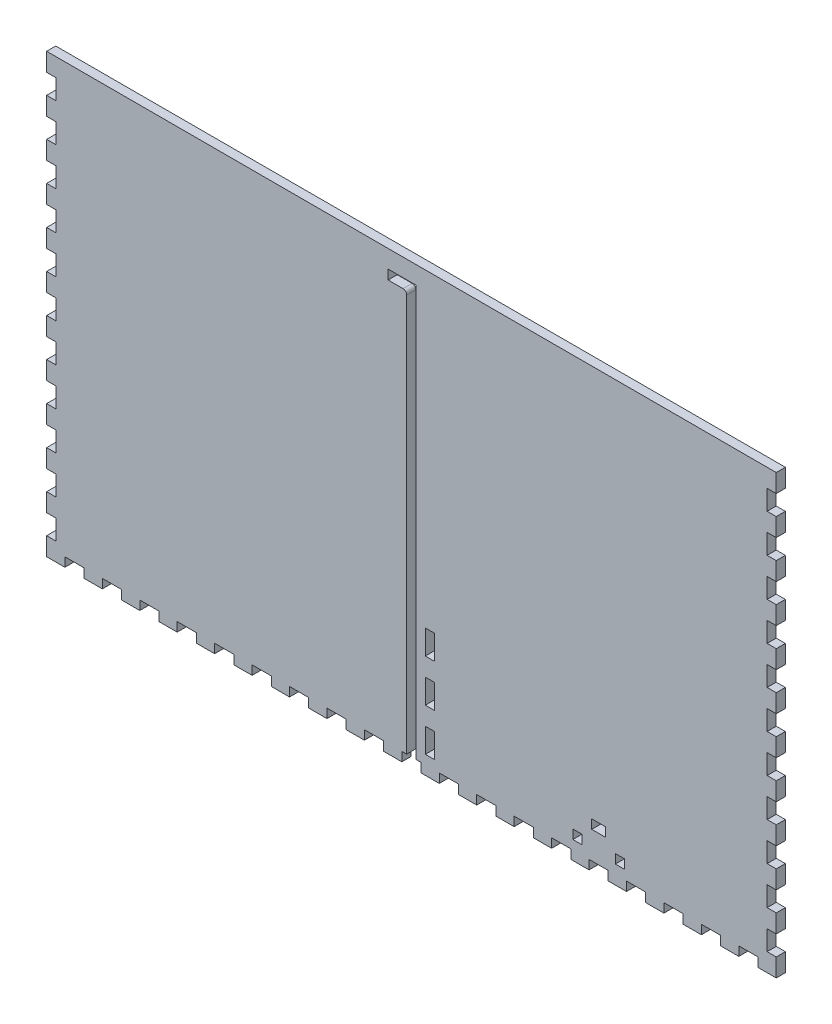
SolidWorks part; units mm, degrees
material "Acrylic (Medium-high impact)"
ref_plane "Front Plane" through (0, 0, 0) normal (0, 0, 1) x (1, 0, 0)
ref_plane "Top Plane" through (0, 0, 0) normal (0, 1, 0) x (1, 0, 0)
ref_plane "Right Plane" through (0, 0, 0) normal (1, 0, 0) x (0, 0, -1)
sketch "Sketch1" plane through (0, 0, 0) normal (0, 1, 0) x (1, 0, 0)
  line L1 (-254, 95.25) -> (254, 95.25)
  line L2 (-254, 95.25) -> (-254, -95.25)
  line L3 (-254, -95.25) -> (254, -95.25)
  line L4 (254, 95.25) -> (254, -95.25)
  point P4 (-254, 0)
  point P6 (0, 95.25)
  dimension "D1" = 190.5
  dimension "D2" = 508
extrude "Boss-Extrude1" add sketch "Sketch1" along normal blind 6.35
sketch "Sketch2" plane through (0, 6.35, 0) normal (0, 1, 0) x (1, 0, 0)
  line L0 (254, -95.25) -> (254, 95.25) construction
  line L1 (-254, 95.25) -> (254, 95.25)
  line L2 (-254, 95.25) -> (-254, -95.25)
  line L3 (-254, -95.25) -> (254, -95.25)
  line L4 (254, 95.25) -> (254, -95.25)
  line L5 (-254, -95.25) -> (254, -95.25) construction
  line L7 (-247.65, 88.9) -> (247.65, 88.9)
  line L8 (-247.65, 88.9) -> (-247.65, -88.9)
  line L9 (-247.65, -88.9) -> (247.65, -88.9)
  line L10 (247.65, 88.9) -> (247.65, -88.9)
  point P7 (-247.65, 0)
  point P14 (-254, 0)
  point P15 (0, -88.9)
  point P16 (0, -95.25)
  point P17 (247.65, 0)
  point P18 (254, 0)
  dimension "D1" = 6.35
  dimension "D2" = 6.35
extrude "Boss-Extrude2" add sketch "Sketch2" along normal blind 298.45
sketch "Sketch3" plane through (0, 0, 95.25) normal (0, 0, 1) x (1, 0, 0)
  line L0 (0, 304.8) -> (0, 0) construction
  line L1 (-254, 304.8) -> (254, 304.8) construction
  line L2 (-247.65, 6.35) -> (247.65, 6.35) construction
  line L4 (-3.302, 283.21) -> (-3.302, 6.35)
  line L5 (-3.302, 6.35) -> (3.302, 6.35)
  line L6 (3.302, 292.354) -> (3.302, 6.35)
  line L7 (3.302, 292.354) -> (-16.256, 292.354)
  line L9 (-5.842, 285.75) -> (-16.256, 285.75)
  line L10 (-16.256, 292.354) -> (-16.256, 285.75)
  line L11 (3.302, 101.6) -> (16.002, 101.6) construction
  line L12 (-254, 0) -> (254, 0) construction
  line L13 (12.827, 88.9) -> (12.827, 101.6) construction
  line L14 (9.652, 88.9) -> (16.002, 88.9)
  line L15 (9.652, 88.9) -> (9.652, 71.9667)
  line L16 (9.652, 71.9667) -> (16.002, 71.9667)
  line L17 (16.002, 88.9) -> (16.002, 71.9667)
  line L18 (9.652, 42.3333) -> (16.002, 42.3333)
  line L19 (9.652, 42.3333) -> (9.652, 59.2667)
  line L20 (9.652, 59.2667) -> (16.002, 59.2667)
  line L21 (16.002, 42.3333) -> (16.002, 59.2667)
  line L26 (9.652, 29.6333) -> (16.002, 29.6333)
  line L27 (9.652, 29.6333) -> (9.652, 12.7)
  line L28 (9.652, 12.7) -> (16.002, 12.7)
  line L29 (16.002, 29.6333) -> (16.002, 12.7)
  line L30 (12.827, 59.2667) -> (12.827, 71.9667) construction
  line L31 (12.827, 29.6333) -> (12.827, 42.3333) construction
  line L32 (12.827, 12.7) -> (12.827, 0) construction
  arc A0 (-3.302, 283.21) -> (-5.842, 285.75) centre (-5.842, 283.21) ccw
  point P5 (0, 6.35)
  dimension "D5" = 2.54
  dimension "D1" = 6.604
  dimension "D2" = 12.954
  dimension "D3" = 6.604
  dimension "D4" = 286.004
  dimension "D6" = 101.6
  dimension "D7" = 12.7
  dimension "D8" = 12.7
  dimension "D9" = 6.35
extrude "Cut-Extrude1" cut sketch "Sketch3" against normal blind 12.7
sketch "Sketch4" plane through (0, 0, -88.9) normal (0, 0, 1) x (1, 0, 0)
  line L0 (-254, 304.8) -> (254, 304.8) construction
  line L1 (-22.606, 304.8) -> (-16.256, 304.8)
  line L2 (-22.606, 304.8) -> (-22.606, 6.35)
  line L3 (-22.606, 6.35) -> (-16.256, 6.35)
  line L4 (-16.256, 304.8) -> (-16.256, 6.35)
  line L5 (6.477, 263.525) -> (6.477, 247.65) construction
  line L6 (-16.256, 292.354) -> (-16.256, 285.75) construction
  line L7 (3.302, 304.8) -> (9.652, 304.8)
  line L8 (3.302, 304.8) -> (3.302, 6.35)
  line L9 (3.302, 6.35) -> (9.652, 6.35)
  line L10 (9.652, 304.8) -> (9.652, 6.35)
  line L11 (247.65, 6.35) -> (-247.65, 6.35) construction
  line L12 (3.302, 6.35) -> (3.302, 292.354) construction
  line L13 (-16.256, 304.8) -> (-22.606, 304.8)
  line L14 (-16.256, 304.8) -> (-16.256, 292.1)
  line L15 (-16.256, 292.1) -> (-22.606, 292.1)
  line L16 (-22.606, 304.8) -> (-22.606, 292.1)
  line L17 (-16.256, 276.225) -> (-22.606, 276.225)
  line L18 (-16.256, 276.225) -> (-16.256, 263.525)
  line L19 (-16.256, 263.525) -> (-22.606, 263.525)
  line L20 (-22.606, 276.225) -> (-22.606, 263.525)
  line L21 (-22.606, 6.35) -> (-16.256, 6.35)
  line L22 (-22.606, 6.35) -> (-22.606, 19.05)
  line L23 (-22.606, 19.05) -> (-16.256, 19.05)
  line L24 (-16.256, 6.35) -> (-16.256, 19.05)
  line L25 (-22.606, 34.925) -> (-16.256, 34.925)
  line L26 (-22.606, 34.925) -> (-22.606, 47.625)
  line L27 (-22.606, 47.625) -> (-16.256, 47.625)
  line L28 (-16.256, 34.925) -> (-16.256, 47.625)
  line L29 (-22.606, 92.075) -> (-16.256, 92.075)
  line L30 (-22.606, 92.075) -> (-22.606, 104.775)
  line L31 (-22.606, 104.775) -> (-16.256, 104.775)
  line L32 (-16.256, 92.075) -> (-16.256, 104.775)
  line L33 (-22.606, 149.225) -> (-16.256, 149.225)
  line L34 (-22.606, 149.225) -> (-22.606, 161.925)
  line L35 (-22.606, 161.925) -> (-16.256, 161.925)
  line L36 (-16.256, 149.225) -> (-16.256, 161.925)
  line L37 (-22.606, 177.8) -> (-16.256, 177.8)
  line L38 (-22.606, 177.8) -> (-22.606, 190.5)
  line L39 (-22.606, 190.5) -> (-16.256, 190.5)
  line L40 (-16.256, 177.8) -> (-16.256, 190.5)
  line L41 (-22.606, 206.375) -> (-16.256, 206.375)
  line L42 (-22.606, 206.375) -> (-22.606, 219.075)
  line L43 (-22.606, 219.075) -> (-16.256, 219.075)
  line L44 (-16.256, 206.375) -> (-16.256, 219.075)
  line L45 (-22.606, 234.95) -> (-16.256, 234.95)
  line L46 (-22.606, 234.95) -> (-22.606, 247.65)
  line L47 (-22.606, 247.65) -> (-16.256, 247.65)
  line L48 (-16.256, 234.95) -> (-16.256, 247.65)
  line L49 (-16.256, 133.35) -> (-22.606, 133.35)
  line L50 (-16.256, 133.35) -> (-16.256, 120.65)
  line L51 (-16.256, 120.65) -> (-22.606, 120.65)
  line L52 (-22.606, 133.35) -> (-22.606, 120.65)
  line L53 (-16.256, 76.2) -> (-22.606, 76.2)
  line L54 (-16.256, 76.2) -> (-16.256, 63.5)
  line L55 (-16.256, 63.5) -> (-22.606, 63.5)
  line L56 (-22.606, 76.2) -> (-22.606, 63.5)
  line L57 (-19.431, 304.8) -> (-19.431, 292.1) construction
  line L58 (-19.431, 292.1) -> (-19.431, 276.225) construction
  line L59 (-19.431, 276.225) -> (-19.431, 263.525) construction
  line L60 (-19.431, 247.65) -> (-19.431, 234.95) construction
  line L61 (-19.431, 234.95) -> (-19.431, 219.075) construction
  line L62 (-19.431, 219.075) -> (-19.431, 206.375) construction
  line L63 (-19.431, 206.375) -> (-19.431, 190.5) construction
  line L64 (-19.431, 190.5) -> (-19.431, 177.8) construction
  line L65 (-19.431, 177.8) -> (-19.431, 161.925) construction
  line L66 (-19.431, 161.925) -> (-19.431, 149.225) construction
  line L67 (-19.431, 133.35) -> (-19.431, 120.65) construction
  line L68 (-19.431, 120.65) -> (-19.431, 104.775) construction
  line L69 (-19.431, 104.775) -> (-19.431, 92.075) construction
  line L70 (-19.431, 92.075) -> (-19.431, 76.2) construction
  line L71 (-19.431, 76.2) -> (-19.431, 63.5) construction
  line L72 (-19.431, 63.5) -> (-19.431, 47.625) construction
  line L73 (-19.431, 47.625) -> (-19.431, 34.925) construction
  line L74 (-19.431, 34.925) -> (-19.431, 19.05) construction
  line L75 (-19.431, 19.05) -> (-19.431, 6.35) construction
  line L76 (-19.431, 149.225) -> (-19.431, 133.35) construction
  line L77 (-19.431, 263.525) -> (-19.431, 247.65) construction
  line L78 (-6.477, 304.8) -> (-6.477, 0) construction
  line L79 (254, 304.8) -> (-254, 304.8) construction
  line L80 (254, 0) -> (-254, 0) construction
  line L81 (-6.477, 8.3493) -> (3.302, 8.3493) construction
  line L82 (-6.477, 8.3493) -> (-16.256, 8.3493) construction
  line L83 (6.477, 149.225) -> (6.477, 133.35) construction
  line L84 (6.477, 19.05) -> (6.477, 6.35) construction
  line L85 (6.477, 34.925) -> (6.477, 19.05) construction
  line L86 (6.477, 47.625) -> (6.477, 34.925) construction
  line L87 (6.477, 63.5) -> (6.477, 47.625) construction
  line L88 (6.477, 76.2) -> (6.477, 63.5) construction
  line L89 (6.477, 92.075) -> (6.477, 76.2) construction
  line L90 (6.477, 104.775) -> (6.477, 92.075) construction
  line L91 (6.477, 120.65) -> (6.477, 104.775) construction
  line L92 (6.477, 133.35) -> (6.477, 120.65) construction
  line L93 (6.477, 161.925) -> (6.477, 149.225) construction
  line L94 (6.477, 177.8) -> (6.477, 161.925) construction
  line L95 (6.477, 190.5) -> (6.477, 177.8) construction
  line L96 (6.477, 206.375) -> (6.477, 190.5) construction
  line L97 (6.477, 219.075) -> (6.477, 206.375) construction
  line L98 (6.477, 234.95) -> (6.477, 219.075) construction
  line L99 (6.477, 247.65) -> (6.477, 234.95) construction
  line L100 (6.477, 276.225) -> (6.477, 263.525) construction
  line L101 (6.477, 292.1) -> (6.477, 276.225) construction
  line L102 (6.477, 304.8) -> (6.477, 292.1) construction
  line L103 (9.652, 76.2) -> (9.652, 63.5)
  line L104 (3.302, 63.5) -> (9.652, 63.5)
  line L105 (3.302, 76.2) -> (3.302, 63.5)
  line L106 (3.302, 76.2) -> (9.652, 76.2)
  line L107 (9.652, 133.35) -> (9.652, 120.65)
  line L108 (3.302, 120.65) -> (9.652, 120.65)
  line L109 (3.302, 133.35) -> (3.302, 120.65)
  line L110 (3.302, 133.35) -> (9.652, 133.35)
  line L111 (3.302, 234.95) -> (3.302, 247.65)
  line L112 (9.652, 247.65) -> (3.302, 247.65)
  line L113 (9.652, 234.95) -> (9.652, 247.65)
  line L114 (9.652, 234.95) -> (3.302, 234.95)
  line L115 (3.302, 206.375) -> (3.302, 219.075)
  line L116 (9.652, 219.075) -> (3.302, 219.075)
  line L117 (9.652, 206.375) -> (9.652, 219.075)
  line L118 (9.652, 206.375) -> (3.302, 206.375)
  line L119 (3.302, 177.8) -> (3.302, 190.5)
  line L120 (9.652, 190.5) -> (3.302, 190.5)
  line L121 (9.652, 177.8) -> (9.652, 190.5)
  line L122 (9.652, 177.8) -> (3.302, 177.8)
  line L123 (3.302, 149.225) -> (3.302, 161.925)
  line L124 (9.652, 161.925) -> (3.302, 161.925)
  line L125 (9.652, 149.225) -> (9.652, 161.925)
  line L126 (9.652, 149.225) -> (3.302, 149.225)
  line L127 (3.302, 92.075) -> (3.302, 104.775)
  line L128 (9.652, 104.775) -> (3.302, 104.775)
  line L129 (9.652, 92.075) -> (9.652, 104.775)
  line L130 (9.652, 92.075) -> (3.302, 92.075)
  line L131 (3.302, 34.925) -> (3.302, 47.625)
  line L132 (9.652, 47.625) -> (3.302, 47.625)
  line L133 (9.652, 34.925) -> (9.652, 47.625)
  line L134 (9.652, 34.925) -> (3.302, 34.925)
  line L135 (3.302, 6.35) -> (3.302, 19.05)
  line L136 (9.652, 19.05) -> (3.302, 19.05)
  line L137 (9.652, 6.35) -> (9.652, 19.05)
  line L138 (9.652, 6.35) -> (3.302, 6.35)
  line L139 (9.652, 276.225) -> (9.652, 263.525)
  line L140 (3.302, 263.525) -> (9.652, 263.525)
  line L141 (3.302, 276.225) -> (3.302, 263.525)
  line L142 (3.302, 276.225) -> (9.652, 276.225)
  line L143 (9.652, 304.8) -> (9.652, 292.1)
  line L144 (3.302, 292.1) -> (9.652, 292.1)
  line L145 (3.302, 304.8) -> (3.302, 292.1)
  line L146 (3.302, 304.8) -> (9.652, 304.8)
  line L147 (3.302, 304.8) -> (3.302, 6.35)
  line L148 (9.652, 6.35) -> (3.302, 6.35)
  line L149 (9.652, 304.8) -> (9.652, 6.35)
  line L150 (9.652, 304.8) -> (3.302, 304.8)
  point P14 (-16.256, 289.052)
  dimension "D1" = 6.35
  dimension "D2" = 12.7
extrude "Cut-Extrude2" cut sketch "Sketch4" against normal up to next (6.35 mm away) contours L17 L4 L15 L2 | L2 L47 L4 L19 | L45 L2 L43 L4 | L41 L2 L39 L4 | L37 L2 L35 L4 | L49 L4 L33 L2 | L4 L51 L2 L31 | L53 L4 L29 L2 | L4 L55 L2 L27 | L25 L2 L23 L4
ref_plane "Plane1" through (-6.477, 0, 0) normal (-1, 0, 0) x (0, 0, 1)
mirror "Mirror1" about plane through (-6.477, 0, 0) normal (-1, 0, 0) of "Cut-Extrude2"
sketch "Sketch5" plane through (0, 0, 0) normal (0, -1, 0) x (-1, 0, 0)
  line L0 (-227.9316, -95.25) -> (-227.9316, -88.9)
  line L1 (-247.65, 88.9) -> (247.65, 88.9)
  line L2 (-247.65, 88.9) -> (-247.65, -88.9)
  line L3 (-247.65, -88.9) -> (247.65, -88.9)
  line L4 (247.65, 88.9) -> (247.65, -88.9)
  line L5 (-254, -95.25) -> (-241.3, -95.25)
  line L6 (-254, -95.25) -> (-254, -88.9)
  line L7 (-254, -88.9) -> (-241.3, -88.9)
  line L8 (-241.3, -95.25) -> (-241.3, -88.9)
  line L9 (-227.9316, -95.25) -> (-215.2316, -95.25)
  line L10 (-227.9316, -88.9) -> (-215.2316, -88.9)
  line L11 (-215.2316, -95.25) -> (-215.2316, -88.9)
  line L12 (-201.8632, -95.25) -> (-201.8632, -88.9)
  line L13 (-201.8632, -95.25) -> (-189.1632, -95.25)
  line L14 (-201.8632, -88.9) -> (-189.1632, -88.9)
  line L15 (-189.1632, -95.25) -> (-189.1632, -88.9)
  line L16 (-175.7947, -95.25) -> (-175.7947, -88.9)
  line L17 (-175.7947, -95.25) -> (-163.0947, -95.25)
  line L18 (-175.7947, -88.9) -> (-163.0947, -88.9)
  line L19 (-163.0947, -95.25) -> (-163.0947, -88.9)
  line L20 (-149.7263, -95.25) -> (-149.7263, -88.9)
  line L21 (-149.7263, -95.25) -> (-137.0263, -95.25)
  line L22 (-149.7263, -88.9) -> (-137.0263, -88.9)
  line L23 (-137.0263, -95.25) -> (-137.0263, -88.9)
  line L24 (-123.6579, -95.25) -> (-123.6579, -88.9)
  line L25 (-123.6579, -95.25) -> (-110.9579, -95.25)
  line L26 (-123.6579, -88.9) -> (-110.9579, -88.9)
  line L27 (-110.9579, -95.25) -> (-110.9579, -88.9)
  line L28 (-97.5895, -95.25) -> (-97.5895, -88.9)
  line L29 (-97.5895, -95.25) -> (-84.8895, -95.25)
  line L30 (-97.5895, -88.9) -> (-84.8895, -88.9)
  line L31 (-84.8895, -95.25) -> (-84.8895, -88.9)
  line L32 (-71.5211, -95.25) -> (-71.5211, -88.9)
  line L33 (-71.5211, -95.25) -> (-58.8211, -95.25)
  line L34 (-71.5211, -88.9) -> (-58.8211, -88.9)
  line L35 (-58.8211, -95.25) -> (-58.8211, -88.9)
  line L36 (-45.4526, -95.25) -> (-45.4526, -88.9)
  line L37 (-45.4526, -95.25) -> (-32.7526, -95.25)
  line L38 (-45.4526, -88.9) -> (-32.7526, -88.9)
  line L39 (-32.7526, -95.25) -> (-32.7526, -88.9)
  line L40 (-19.3842, -95.25) -> (-19.3842, -88.9)
  line L41 (-19.3842, -95.25) -> (-6.6842, -95.25)
  line L42 (-19.3842, -88.9) -> (-6.6842, -88.9)
  line L43 (-6.6842, -95.25) -> (-6.6842, -88.9)
  line L44 (6.6842, -95.25) -> (6.6842, -88.9)
  line L45 (6.6842, -95.25) -> (19.3842, -95.25)
  line L46 (6.6842, -88.9) -> (19.3842, -88.9)
  line L47 (19.3842, -95.25) -> (19.3842, -88.9)
  line L48 (32.7526, -95.25) -> (32.7526, -88.9)
  line L49 (32.7526, -95.25) -> (45.4526, -95.25)
  line L50 (32.7526, -88.9) -> (45.4526, -88.9)
  line L51 (45.4526, -95.25) -> (45.4526, -88.9)
  line L52 (58.8211, -95.25) -> (58.8211, -88.9)
  line L53 (58.8211, -95.25) -> (71.5211, -95.25)
  line L54 (58.8211, -88.9) -> (71.5211, -88.9)
  line L55 (71.5211, -95.25) -> (71.5211, -88.9)
  line L56 (84.8895, -95.25) -> (84.8895, -88.9)
  line L57 (84.8895, -95.25) -> (97.5895, -95.25)
  line L58 (84.8895, -88.9) -> (97.5895, -88.9)
  line L59 (97.5895, -95.25) -> (97.5895, -88.9)
  line L60 (110.9579, -95.25) -> (110.9579, -88.9)
  line L61 (110.9579, -95.25) -> (123.6579, -95.25)
  line L62 (110.9579, -88.9) -> (123.6579, -88.9)
  line L63 (123.6579, -95.25) -> (123.6579, -88.9)
  line L64 (137.0263, -95.25) -> (137.0263, -88.9)
  line L65 (137.0263, -95.25) -> (149.7263, -95.25)
  line L66 (137.0263, -88.9) -> (149.7263, -88.9)
  line L67 (149.7263, -95.25) -> (149.7263, -88.9)
  line L68 (163.0947, -95.25) -> (163.0947, -88.9)
  line L69 (163.0947, -95.25) -> (175.7947, -95.25)
  line L70 (163.0947, -88.9) -> (175.7947, -88.9)
  line L71 (175.7947, -95.25) -> (175.7947, -88.9)
  line L72 (189.1632, -95.25) -> (189.1632, -88.9)
  line L73 (189.1632, -95.25) -> (201.8632, -95.25)
  line L74 (189.1632, -88.9) -> (201.8632, -88.9)
  line L75 (201.8632, -95.25) -> (201.8632, -88.9)
  line L76 (215.2316, -95.25) -> (215.2316, -88.9)
  line L77 (215.2316, -95.25) -> (227.9316, -95.25)
  line L78 (215.2316, -88.9) -> (227.9316, -88.9)
  line L79 (227.9316, -95.25) -> (227.9316, -88.9)
  line L80 (241.3, -95.25) -> (241.3, -88.9)
  line L81 (241.3, -95.25) -> (254, -95.25)
  line L82 (241.3, -88.9) -> (254, -88.9)
  line L83 (254, -95.25) -> (254, -88.9)
  line L84 (-167.64, 0) -> (167.64, 0) construction
  line L85 (254, 95.25) -> (254, 88.9)
  line L86 (241.3, 88.9) -> (254, 88.9)
  line L87 (241.3, 95.25) -> (254, 95.25)
  line L88 (241.3, 95.25) -> (241.3, 88.9)
  line L89 (227.9316, 95.25) -> (227.9316, 88.9)
  line L90 (215.2316, 88.9) -> (227.9316, 88.9)
  line L91 (215.2316, 95.25) -> (227.9316, 95.25)
  line L92 (215.2316, 95.25) -> (215.2316, 88.9)
  line L93 (201.8632, 95.25) -> (201.8632, 88.9)
  line L94 (189.1632, 88.9) -> (201.8632, 88.9)
  line L95 (189.1632, 95.25) -> (201.8632, 95.25)
  line L96 (189.1632, 95.25) -> (189.1632, 88.9)
  line L97 (175.7947, 95.25) -> (175.7947, 88.9)
  line L98 (163.0947, 88.9) -> (175.7947, 88.9)
  line L99 (163.0947, 95.25) -> (175.7947, 95.25)
  line L100 (163.0947, 95.25) -> (163.0947, 88.9)
  line L101 (149.7263, 95.25) -> (149.7263, 88.9)
  line L102 (137.0263, 88.9) -> (149.7263, 88.9)
  line L103 (137.0263, 95.25) -> (149.7263, 95.25)
  line L104 (137.0263, 95.25) -> (137.0263, 88.9)
  line L105 (123.6579, 95.25) -> (123.6579, 88.9)
  line L106 (110.9579, 88.9) -> (123.6579, 88.9)
  line L107 (110.9579, 95.25) -> (123.6579, 95.25)
  line L108 (110.9579, 95.25) -> (110.9579, 88.9)
  line L109 (97.5895, 95.25) -> (97.5895, 88.9)
  line L110 (84.8895, 88.9) -> (97.5895, 88.9)
  line L111 (84.8895, 95.25) -> (97.5895, 95.25)
  line L112 (84.8895, 95.25) -> (84.8895, 88.9)
  line L113 (71.5211, 95.25) -> (71.5211, 88.9)
  line L114 (58.8211, 88.9) -> (71.5211, 88.9)
  line L115 (58.8211, 95.25) -> (71.5211, 95.25)
  line L116 (58.8211, 95.25) -> (58.8211, 88.9)
  line L117 (45.4526, 95.25) -> (45.4526, 88.9)
  line L118 (32.7526, 88.9) -> (45.4526, 88.9)
  line L119 (32.7526, 95.25) -> (45.4526, 95.25)
  line L120 (32.7526, 95.25) -> (32.7526, 88.9)
  line L121 (19.3842, 95.25) -> (19.3842, 88.9)
  line L122 (6.6842, 88.9) -> (19.3842, 88.9)
  line L123 (6.6842, 95.25) -> (19.3842, 95.25)
  line L124 (6.6842, 95.25) -> (6.6842, 88.9)
  line L125 (-6.6842, 95.25) -> (-6.6842, 88.9)
  line L126 (-19.3842, 88.9) -> (-6.6842, 88.9)
  line L127 (-19.3842, 95.25) -> (-6.6842, 95.25)
  line L128 (-19.3842, 95.25) -> (-19.3842, 88.9)
  line L129 (-32.7526, 95.25) -> (-32.7526, 88.9)
  line L130 (-45.4526, 88.9) -> (-32.7526, 88.9)
  line L131 (-45.4526, 95.25) -> (-32.7526, 95.25)
  line L132 (-45.4526, 95.25) -> (-45.4526, 88.9)
  line L133 (-58.8211, 95.25) -> (-58.8211, 88.9)
  line L134 (-71.5211, 88.9) -> (-58.8211, 88.9)
  line L135 (-71.5211, 95.25) -> (-58.8211, 95.25)
  line L136 (-71.5211, 95.25) -> (-71.5211, 88.9)
  line L137 (-84.8895, 95.25) -> (-84.8895, 88.9)
  line L138 (-97.5895, 88.9) -> (-84.8895, 88.9)
  line L139 (-97.5895, 95.25) -> (-84.8895, 95.25)
  line L140 (-97.5895, 95.25) -> (-97.5895, 88.9)
  line L141 (-110.9579, 95.25) -> (-110.9579, 88.9)
  line L142 (-123.6579, 88.9) -> (-110.9579, 88.9)
  line L143 (-123.6579, 95.25) -> (-110.9579, 95.25)
  line L144 (-123.6579, 95.25) -> (-123.6579, 88.9)
  line L145 (-137.0263, 95.25) -> (-137.0263, 88.9)
  line L146 (-149.7263, 88.9) -> (-137.0263, 88.9)
  line L147 (-149.7263, 95.25) -> (-137.0263, 95.25)
  line L148 (-149.7263, 95.25) -> (-149.7263, 88.9)
  line L149 (-163.0947, 95.25) -> (-163.0947, 88.9)
  line L150 (-175.7947, 88.9) -> (-163.0947, 88.9)
  line L151 (-175.7947, 95.25) -> (-163.0947, 95.25)
  line L152 (-175.7947, 95.25) -> (-175.7947, 88.9)
  line L153 (-189.1632, 95.25) -> (-189.1632, 88.9)
  line L154 (-201.8632, 88.9) -> (-189.1632, 88.9)
  line L155 (-201.8632, 95.25) -> (-189.1632, 95.25)
  line L156 (-201.8632, 95.25) -> (-201.8632, 88.9)
  line L157 (-215.2316, 95.25) -> (-215.2316, 88.9)
  line L158 (-227.9316, 88.9) -> (-215.2316, 88.9)
  line L159 (-227.9316, 95.25) -> (-215.2316, 95.25)
  line L160 (-241.3, 95.25) -> (-241.3, 88.9)
  line L161 (-254, 88.9) -> (-241.3, 88.9)
  line L162 (-254, 95.25) -> (-254, 88.9)
  line L163 (-254, 95.25) -> (-241.3, 95.25)
  line L164 (-247.65, 88.9) -> (247.65, 88.9)
  line L165 (-227.9316, 95.25) -> (-227.9316, 88.9)
  line L166 (-254, 65.6167) -> (-254, 52.9167)
  line L167 (-254, 95.25) -> (-247.65, 95.25)
  line L168 (-254, 95.25) -> (-254, 82.55)
  line L169 (-254, 82.55) -> (-247.65, 82.55)
  line L170 (-247.65, 95.25) -> (-247.65, 82.55)
  line L171 (-254, 65.6167) -> (-247.65, 65.6167)
  line L172 (-247.65, 65.6167) -> (-247.65, 52.9167)
  line L173 (-254, 52.9167) -> (-247.65, 52.9167)
  line L174 (-254, 35.9833) -> (-254, 23.2833)
  line L175 (-254, 35.9833) -> (-247.65, 35.9833)
  line L176 (-247.65, 35.9833) -> (-247.65, 23.2833)
  line L177 (-254, 23.2833) -> (-247.65, 23.2833)
  line L178 (-254, 6.35) -> (-254, -6.35)
  line L179 (-254, 6.35) -> (-247.65, 6.35)
  line L180 (-247.65, 6.35) -> (-247.65, -6.35)
  line L181 (-254, -6.35) -> (-247.65, -6.35)
  line L182 (-254, -23.2833) -> (-254, -35.9833)
  line L183 (-254, -23.2833) -> (-247.65, -23.2833)
  line L184 (-247.65, -23.2833) -> (-247.65, -35.9833)
  line L185 (-254, -35.9833) -> (-247.65, -35.9833)
  line L186 (-254, -52.9167) -> (-254, -65.6167)
  line L187 (-254, -52.9167) -> (-247.65, -52.9167)
  line L188 (-247.65, -52.9167) -> (-247.65, -65.6167)
  line L189 (-254, -65.6167) -> (-247.65, -65.6167)
  line L190 (-254, -82.55) -> (-254, -95.25)
  line L191 (-254, -82.55) -> (-247.65, -82.55)
  line L192 (-247.65, -82.55) -> (-247.65, -95.25)
  line L193 (-254, -95.25) -> (-247.65, -95.25)
  line L194 (0, 104.775) -> (0, -104.775) construction
  line L195 (254, -95.25) -> (247.65, -95.25)
  line L196 (247.65, -82.55) -> (247.65, -95.25)
  line L197 (254, -82.55) -> (247.65, -82.55)
  line L198 (254, -82.55) -> (254, -95.25)
  line L199 (254, -65.6167) -> (247.65, -65.6167)
  line L200 (247.65, -52.9167) -> (247.65, -65.6167)
  line L201 (254, -52.9167) -> (247.65, -52.9167)
  line L202 (254, -52.9167) -> (254, -65.6167)
  line L203 (254, -35.9833) -> (247.65, -35.9833)
  line L204 (247.65, -23.2833) -> (247.65, -35.9833)
  line L205 (254, -23.2833) -> (247.65, -23.2833)
  line L206 (254, -23.2833) -> (254, -35.9833)
  line L207 (254, -6.35) -> (247.65, -6.35)
  line L208 (247.65, 6.35) -> (247.65, -6.35)
  line L209 (254, 6.35) -> (247.65, 6.35)
  line L210 (254, 6.35) -> (254, -6.35)
  line L211 (254, 23.2833) -> (247.65, 23.2833)
  line L212 (247.65, 35.9833) -> (247.65, 23.2833)
  line L213 (254, 35.9833) -> (247.65, 35.9833)
  line L214 (254, 35.9833) -> (254, 23.2833)
  line L215 (254, 52.9167) -> (247.65, 52.9167)
  line L216 (247.65, 65.6167) -> (247.65, 52.9167)
  line L217 (254, 65.6167) -> (247.65, 65.6167)
  line L218 (247.65, 95.25) -> (247.65, 82.55)
  line L219 (254, 82.55) -> (247.65, 82.55)
  line L220 (254, 95.25) -> (254, 82.55)
  line L221 (254, 95.25) -> (247.65, 95.25)
  line L222 (254, 65.6167) -> (254, 52.9167)
  line L223 (254, 95.25) -> (254, 88.9)
  line L224 (254, -95.25) -> (254, -88.9)
  line L225 (247.65, 88.9) -> (247.65, -88.9)
  line M117 (-254, -95.25) -> (254, -95.25)
  dimension "D1" = 12.7
  dimension "D3" = 6.35
  dimension "D5" = 12.7
  dimension "D2" = 20
  dimension "D4" = 7
sketch "Sketch6" plane through (0, 0, 0) normal (0, 1, 0) x (1, 0, 0)
  line L1 (-260.4023, 138.7232) -> (290.7248, 138.7232)
  line L2 (-260.4023, 138.7232) -> (-260.4023, -88.9)
  line L3 (-260.4023, -88.9) -> (290.7248, -88.9)
  line L4 (290.7248, 138.7232) -> (290.7248, -88.9)
  line L5 (3.302, -88.9) -> (247.65, -88.9) construction
extrude "Cut-Extrude5" cut sketch "Sketch6" along normal through all
extrude "Cut-Extrude6" cut sketch "Sketch5" against normal blind 6.35 contours L8 L0 L3 M117 | L12 L3 L11 M117 | L16 L3 L15 M117 | L20 L3 L19 M117 | L24 L3 L23 M117 | L28 L3 L27 M117 | L32 L3 L31 M117 | L36 L3 L35 M117 | L40 L3 L39 M117 | L44 L3 L43 M117 | L48 L3 L47 M117 | L52 L3 L51 M117 | L56 L3 L55 M117 | L60 L3 L59 M117 | L64 L3 L63 M117 | L68 L3 L67 M117 | L72 L3 L71 M117 | L76 L3 L75 M117 | L80 L3 L79 M117
sketch "Sketch7" plane through (254, 0, 0) normal (1, 0, 0) x (0, 0, -1)
  line L0 (-95.25, 26.5545) -> (-95.25, 39.2545)
  line L1 (-95.25, 0) -> (-88.9, 0)
  line L2 (-95.25, 0) -> (-95.25, 12.7)
  line L3 (-95.25, 12.7) -> (-88.9, 12.7)
  line L4 (-88.9, 0) -> (-88.9, 12.7)
  line L5 (-95.25, 26.5545) -> (-88.9, 26.5545)
  line L6 (-88.9, 26.5545) -> (-88.9, 39.2545)
  line L7 (-95.25, 39.2545) -> (-88.9, 39.2545)
  line L8 (-95.25, 53.1091) -> (-95.25, 65.8091)
  line L9 (-95.25, 53.1091) -> (-88.9, 53.1091)
  line L10 (-88.9, 53.1091) -> (-88.9, 65.8091)
  line L11 (-95.25, 65.8091) -> (-88.9, 65.8091)
  line L12 (-95.25, 79.6636) -> (-95.25, 92.3636)
  line L13 (-95.25, 79.6636) -> (-88.9, 79.6636)
  line L14 (-88.9, 79.6636) -> (-88.9, 92.3636)
  line L15 (-95.25, 92.3636) -> (-88.9, 92.3636)
  line L16 (-95.25, 106.2182) -> (-95.25, 118.9182)
  line L17 (-95.25, 106.2182) -> (-88.9, 106.2182)
  line L18 (-88.9, 106.2182) -> (-88.9, 118.9182)
  line L19 (-95.25, 118.9182) -> (-88.9, 118.9182)
  line L20 (-95.25, 132.7727) -> (-95.25, 145.4727)
  line L21 (-95.25, 132.7727) -> (-88.9, 132.7727)
  line L22 (-88.9, 132.7727) -> (-88.9, 145.4727)
  line L23 (-95.25, 145.4727) -> (-88.9, 145.4727)
  line L24 (-95.25, 159.3273) -> (-95.25, 172.0273)
  line L25 (-95.25, 159.3273) -> (-88.9, 159.3273)
  line L26 (-88.9, 159.3273) -> (-88.9, 172.0273)
  line L27 (-95.25, 172.0273) -> (-88.9, 172.0273)
  line L28 (-95.25, 185.8818) -> (-95.25, 198.5818)
  line L29 (-95.25, 185.8818) -> (-88.9, 185.8818)
  line L30 (-88.9, 185.8818) -> (-88.9, 198.5818)
  line L31 (-95.25, 198.5818) -> (-88.9, 198.5818)
  line L32 (-95.25, 212.4364) -> (-95.25, 225.1364)
  line L33 (-95.25, 212.4364) -> (-88.9, 212.4364)
  line L34 (-88.9, 212.4364) -> (-88.9, 225.1364)
  line L35 (-95.25, 225.1364) -> (-88.9, 225.1364)
  line L36 (-95.25, 238.9909) -> (-95.25, 251.6909)
  line L37 (-95.25, 238.9909) -> (-88.9, 238.9909)
  line L38 (-88.9, 238.9909) -> (-88.9, 251.6909)
  line L39 (-95.25, 251.6909) -> (-88.9, 251.6909)
  line L40 (-95.25, 265.5455) -> (-95.25, 278.2455)
  line L41 (-95.25, 265.5455) -> (-88.9, 265.5455)
  line L42 (-88.9, 265.5455) -> (-88.9, 278.2455)
  line L43 (-95.25, 278.2455) -> (-88.9, 278.2455)
  line L44 (-95.25, 292.1) -> (-95.25, 304.8)
  line L45 (-95.25, 292.1) -> (-88.9, 292.1)
  line L46 (-88.9, 292.1) -> (-88.9, 304.8)
  line L47 (-95.25, 304.8) -> (-88.9, 304.8)
  line L48 (0, 167.64) -> (0, -167.64) construction
  line L49 (95.25, 304.8) -> (88.9, 304.8)
  line L50 (88.9, 292.1) -> (88.9, 304.8)
  line L51 (95.25, 292.1) -> (88.9, 292.1)
  line L52 (95.25, 292.1) -> (95.25, 304.8)
  line L53 (95.25, 278.2455) -> (88.9, 278.2455)
  line L54 (88.9, 265.5455) -> (88.9, 278.2455)
  line L55 (95.25, 265.5455) -> (88.9, 265.5455)
  line L56 (95.25, 265.5455) -> (95.25, 278.2455)
  line L57 (95.25, 251.6909) -> (88.9, 251.6909)
  line L58 (88.9, 238.9909) -> (88.9, 251.6909)
  line L59 (95.25, 238.9909) -> (88.9, 238.9909)
  line L60 (95.25, 238.9909) -> (95.25, 251.6909)
  line L61 (95.25, 225.1364) -> (88.9, 225.1364)
  line L62 (88.9, 212.4364) -> (88.9, 225.1364)
  line L63 (95.25, 212.4364) -> (88.9, 212.4364)
  line L64 (95.25, 212.4364) -> (95.25, 225.1364)
  line L65 (95.25, 198.5818) -> (88.9, 198.5818)
  line L66 (88.9, 185.8818) -> (88.9, 198.5818)
  line L67 (95.25, 185.8818) -> (88.9, 185.8818)
  line L68 (95.25, 185.8818) -> (95.25, 198.5818)
  line L69 (95.25, 172.0273) -> (88.9, 172.0273)
  line L70 (88.9, 159.3273) -> (88.9, 172.0273)
  line L71 (95.25, 159.3273) -> (88.9, 159.3273)
  line L72 (95.25, 159.3273) -> (95.25, 172.0273)
  line L73 (95.25, 145.4727) -> (88.9, 145.4727)
  line L74 (88.9, 132.7727) -> (88.9, 145.4727)
  line L75 (95.25, 132.7727) -> (88.9, 132.7727)
  line L76 (95.25, 132.7727) -> (95.25, 145.4727)
  line L77 (95.25, 118.9182) -> (88.9, 118.9182)
  line L78 (88.9, 106.2182) -> (88.9, 118.9182)
  line L79 (95.25, 106.2182) -> (88.9, 106.2182)
  line L80 (95.25, 106.2182) -> (95.25, 118.9182)
  line L81 (95.25, 92.3636) -> (88.9, 92.3636)
  line L82 (88.9, 79.6636) -> (88.9, 92.3636)
  line L83 (95.25, 79.6636) -> (88.9, 79.6636)
  line L84 (95.25, 79.6636) -> (95.25, 92.3636)
  line L85 (95.25, 65.8091) -> (88.9, 65.8091)
  line L86 (88.9, 53.1091) -> (88.9, 65.8091)
  line L87 (95.25, 53.1091) -> (88.9, 53.1091)
  line L88 (95.25, 53.1091) -> (95.25, 65.8091)
  line L89 (95.25, 39.2545) -> (88.9, 39.2545)
  line L90 (88.9, 26.5545) -> (88.9, 39.2545)
  line L91 (95.25, 26.5545) -> (88.9, 26.5545)
  line L92 (88.9, 0) -> (88.9, 12.7)
  line L93 (95.25, 12.7) -> (88.9, 12.7)
  line L94 (95.25, 0) -> (95.25, 12.7)
  line L95 (95.25, 0) -> (88.9, 0)
  line L96 (95.25, 26.5545) -> (95.25, 39.2545)
  line L98 (-95.25, 304.8) -> (-88.9, 304.8)
  line L99 (-95.25, 304.8) -> (-95.25, 0)
  line L100 (-95.25, 0) -> (-88.9, 0)
  line L101 (-88.9, 304.8) -> (-88.9, 0)
  line M52 (-95.25, 304.8) -> (-95.25, 0)
  line M53 (-88.9, 0) -> (-88.9, 304.8)
  dimension "D1" = 12.7
  dimension "D2" = 6.35
  dimension "D3" = 12
extrude "Cut-Extrude7" cut sketch "Sketch7" against normal blind 6.35 contours L45 L43 M52 M53 | L41 L39 M52 M53 | L37 L35 M52 M53 | L33 L31 M52 M53 | L29 L27 M52 M53 | L25 L23 M52 M53 | L21 L19 M52 M53 | L17 L15 M52 M53 | L13 L11 M52 M53 | L9 L7 M52 M53 | L5 L3 M52 M53
mirror "Mirror2" about plane through (0, 0, 0) normal (1, 0, 0) of "Cut-Extrude7"
sketch "Sketch8" plane through (0, 0, 95.25) normal (0, 0, 1) x (1, 0, 0)
  line L0 (137.0263, 0) -> (149.7263, 0) construction
  line L1 (125.5161, 31.75) -> (135.1681, 31.75)
  line L2 (125.5161, 31.75) -> (125.5161, 25.4)
  line L3 (125.5161, 25.4) -> (135.1681, 25.4)
  line L4 (135.1681, 31.75) -> (135.1681, 25.4)
  line L7 (84.8895, 0) -> (97.5895, 0) construction
  line L8 (112.3716, 19.05) -> (118.7216, 19.05)
  line L9 (112.3716, 19.05) -> (112.3716, 12.7)
  line L10 (112.3716, 12.7) -> (118.7216, 12.7)
  line L11 (118.7216, 19.05) -> (118.7216, 12.7)
  line L12 (141.9626, 19.05) -> (148.3126, 19.05)
  line L13 (141.9626, 19.05) -> (141.9626, 12.7)
  line L14 (141.9626, 12.7) -> (148.3126, 12.7)
  line L15 (148.3126, 19.05) -> (148.3126, 12.7)
  line L16 (118.7216, 15.875) -> (141.9626, 15.875) construction
  line L17 (137.0263, 6.35) -> (123.6579, 6.35) construction
  point P16 (130.3421, 15.875)
  point P17 (130.3421, 25.4)
  point P18 (130.3421, 6.35)
  point P21 (115.5466, 12.7)
  dimension "D1" = 9.652
  dimension "D2" = 6.35
  dimension "D3" = 25.4
  dimension "D5" = 6.35
  dimension "D6" = 6.35
  dimension "D7" = 12.7
  dimension "D8" = 23.241
extrude "Lever Hole" cut sketch "Sketch8" against normal through all
